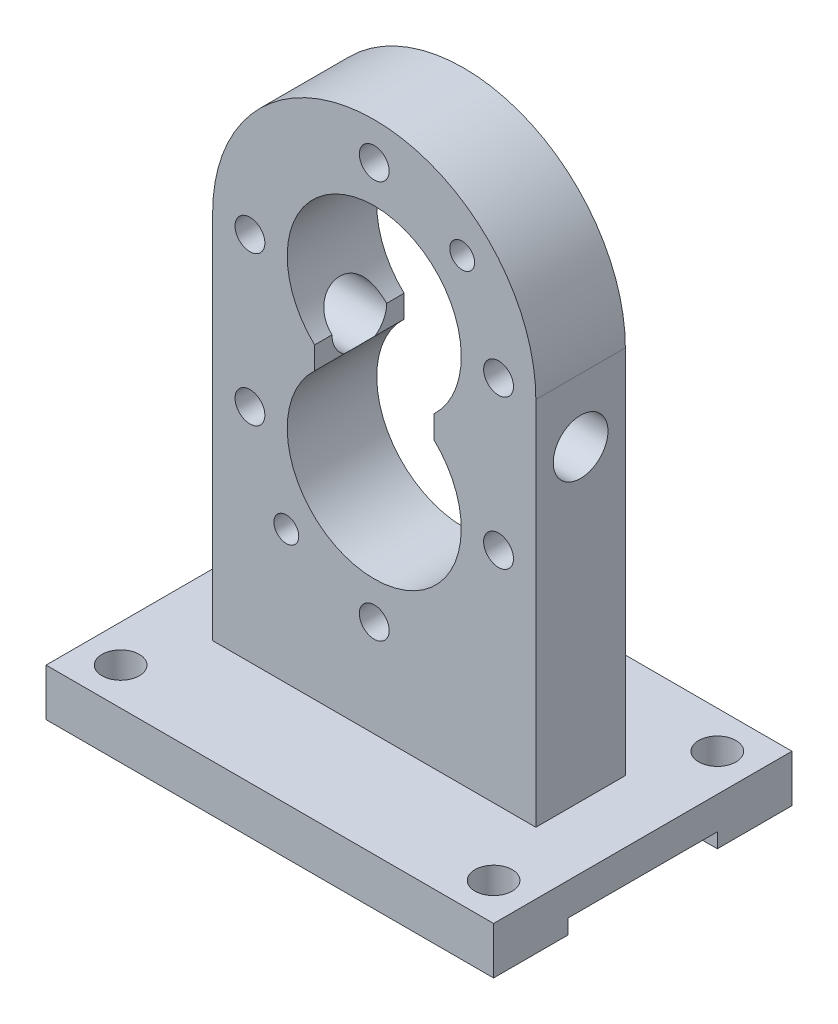
SolidWorks part; units mm, degrees
ref_plane "Front Plane" through (0, 0, 0) normal (0, 0, 1) x (1, 0, 0)
ref_plane "Top Plane" through (0, 0, 0) normal (0, 1, 0) x (1, 0, 0)
ref_plane "Right Plane" through (0, 0, 0) normal (1, 0, 0) x (0, 0, -1)
sketch "Sketch2" plane through (0, 0, 0) normal (0, 1, 0) x (1, 0, 0)
  line L0 (0, 96.5084) -> (0, 0) construction
  line L1 (90, -60) -> (-90, -60)
  line L2 (90, -60) -> (90, 60)
  line L3 (90, 60) -> (-90, 60)
  line L4 (-90, -60) -> (-90, 60)
  line L5 (0, 0) -> (90, 0) construction
  circle A0 centre (-75, 45) radius 7.5
  circle A2 centre (75, 45) radius 7.5
  circle A3 centre (75, -45) radius 7.5
  circle A4 centre (-75, -45) radius 7.5
  point P0 (0, 0)
  dimension "D3" = 15
  dimension "D1" = 180
  dimension "D2" = 120
  dimension "D5" = 15
  dimension "D6" = 15
extrude "Boss-Extrude1" add sketch "Sketch2" along normal mid plane 19
sketch "Sketch14" plane through (0, 0, 0) normal (0, 0, 1) x (1, 0, 0)
  line L0 (0, 122.081) -> (0, 0) construction
  line L1 (-114.1553, 0) -> (0, 0) construction
  line L2 (-65, 9.5) -> (-65, 158.5)
  line L3 (-90, 9.5) -> (90, 9.5) construction
  line L4 (65, 9.5) -> (65, 158.5)
  line L5 (-33.8285, 133.0245) -> (-24, 133.0245) construction
  line L6 (-24, 133.0245) -> (-24, 123.9755)
  line L7 (24, 133.0245) -> (24, 123.9755)
  line L8 (0, 294.919) -> (0, 122.081) construction
  line L9 (-61.7549, 158.5) -> (146.9723, 158.5) construction
  line L10 (-90.2766, 98.5) -> (120.1792, 98.5) construction
  line L11 (-27.4206, 128.5) -> (0, 128.5) construction
  line L12 (-65, 9.5) -> (65, 9.5)
  line L13 (0, 98.5) -> (-54.3791, 44.1209) construction
  line L14 (0, 158.5) -> (81.5955, 240.0955) construction
  line L15 (0, 158.5) -> (195.1491, 158.5) construction
  arc A0 (-65, 158.5) -> (65, 158.5) centre (0, 158.5) cw
  arc A3 (24, 133.0245) -> (-24, 133.0245) centre (0, 158.5) ccw
  arc A4 (-24, 123.9755) -> (24, 123.9755) centre (0, 98.5) ccw
  circle A5 centre (0, 208.5) radius 6
  circle A6 centre (0, 48.5) radius 6
  circle A7 centre (-50, 158.5) radius 6
  circle A8 centre (-50, 98.5) radius 6
  circle A9 centre (50, 98.5) radius 6
  circle A10 centre (50, 158.5) radius 6
  circle A11 centre (-35.36, 63.14) radius 5
  circle A12 centre (35.36, 193.86) radius 5
  dimension "D4" = 65
  dimension "D5" = 70
  dimension "D6" = 60
  dimension "D7" = 48
  dimension "D8" = 12
  dimension "D10" = 12
  dimension "D11" = 12
  dimension "D14" = 45
  dimension "D15" = 10
  dimension "D18" = 10
  dimension "D1" = 65
  dimension "D2" = 149
  dimension "D3" = 130
  dimension "D9" = 50
  dimension "D12" = 60
  dimension "D13" = 15
  dimension "D16" = 29.64
  dimension "D17" = 45
  dimension "D19" = 29.64
extrude "Boss-Extrude5" add sketch "Sketch14" along normal mid plane 36
sketch "Sketch16" plane through (65, 0, 0) normal (1, 0, 0) x (0, 0, -1)
  line L0 (-18, 133.0245) -> (18, 133.0245) construction
  circle A0 centre (0, 133.0245) radius 9
  dimension "D1" = 18
extrude "Cut-Extrude6" cut sketch "Sketch16" against normal through all
sketch "Sketch18" plane through (65, 0, 0) normal (1, 0, 0) x (0, 0, -1)
  circle A0 centre (0, 133.0245) radius 11
  dimension "D1" = 22
extrude "Cut-Extrude7" cut sketch "Sketch18" against normal through all
sketch "Sketch19" plane through (90, 0, 0) normal (1, 0, 0) x (0, 0, -1)
  line L0 (-60, -9.5) -> (60, -9.5) construction
  line L1 (30, -15.4213) -> (-30, -15.4213)
  line L2 (30, -15.4213) -> (30, -3.5787)
  line L3 (30, -3.5787) -> (-30, -3.5787)
  line L4 (-30, -15.4213) -> (-30, -3.5787)
  line L5 (30, -15.4213) -> (-30, -3.5787) construction
  line L6 (30, -3.5787) -> (-30, -15.4213) construction
  point P0 (0, -9.5)
  dimension "D1" = 60
extrude "Cut-Extrude8" cut sketch "Sketch19" against normal through all
